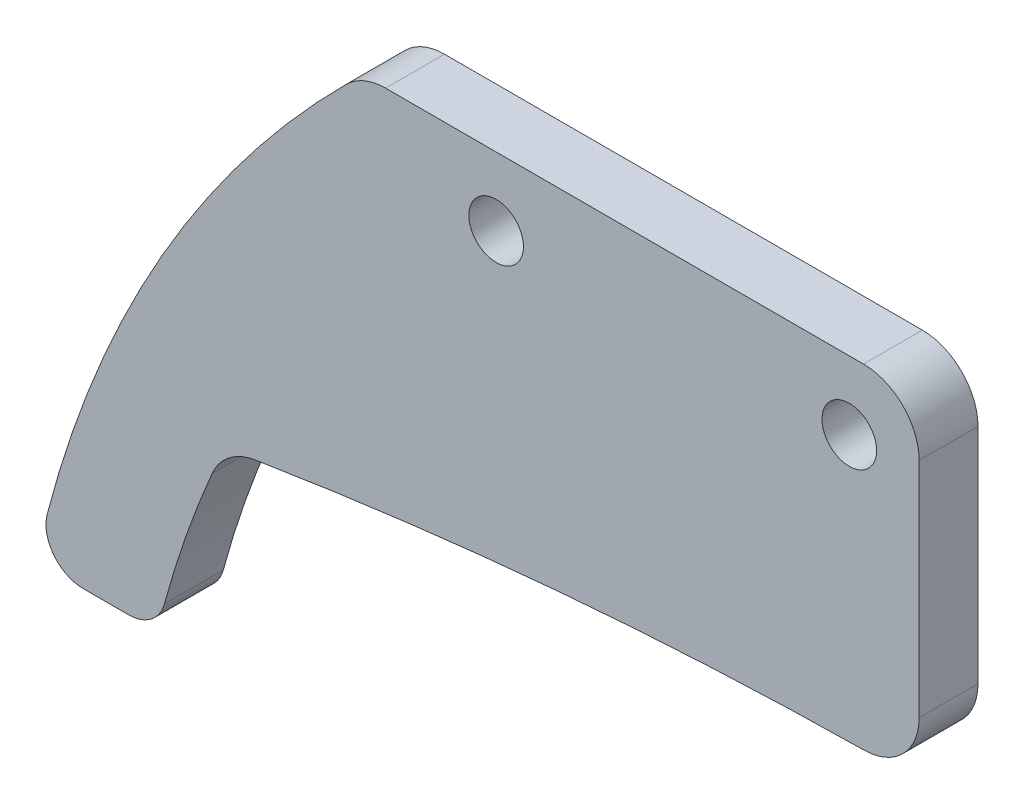
SolidWorks part; units mm, degrees
material "Delrin 2700 NC010, Low Viscosity Acetal Copolymer (SS)"
ref_plane "Front Plane" through (0, 0, 0) normal (0, 0, 1) x (1, 0, 0)
ref_plane "Top Plane" through (0, 0, 0) normal (0, 1, 0) x (1, 0, 0)
ref_plane "Right Plane" through (0, 0, 0) normal (1, 0, 0) x (0, 0, -1)
sketch "Sketch1" plane through (0, 0, 0) normal (0, 0, 1) x (1, 0, 0)
  line L1 (-17.1227, 44.5) -> (-47.1227, 44.5)
  line L3 (-17.1227, 26.5) -> (-17.1227, 44.5)
  line L4 (-17.1227, 26.5) -> (-9.8773, 26.5) construction
  line L7 (-17.1227, 44.5) -> (-47.1227, 44.5)
  line L12 (-58.2093, 12.9656) -> (-64.7502, 12.9656)
  arc A0 (-17.1227, 26.5) -> (-54.5777, 23.3401) centre (-17.1227, -197.0625) ccw
  arc A2 (-47.1227, 44.5) -> (-60.1383, 26.5) centre (-4.5353, 0) ccw
  arc A3 (-47.1227, 44.5) -> (-64.7502, 12.9656) centre (-4.5353, 0) ccw
  arc A4 (-54.5777, 23.3401) -> (-58.2093, 12.9656) centre (-4.5353, 0) ccw
  dimension "D3" = 61.595
  dimension "D2" = 18
  dimension "D1" = 18
  dimension "D4" = 30
extrude "Boss-Extrude1" add sketch "Sketch1" along normal blind 3.175
sketch "Sketch2" plane through (0, 0, 3.175) normal (0, 0, 1) x (1, 0, 0)
  circle A10 centre (-20.8896, 40.8119) radius 1.4732
  circle A11 centre (-39.9396, 40.8119) radius 1.4732
extrude "Cut-Extrude1" cut sketch "Sketch2" against normal through all
fillet "Fillet1" radius 3 4 edges at (-47.1227, 44.5, 1.5875) (-17.1227, 26.5, 1.5875) (-17.1227, 44.5, 1.5875) (-54.5777, 23.3401, 1.5875)
fillet "Fillet3" radius 2 2 edges at (-64.7502, 12.9656, 1.5875) (-58.2093, 12.9656, 1.5875)
